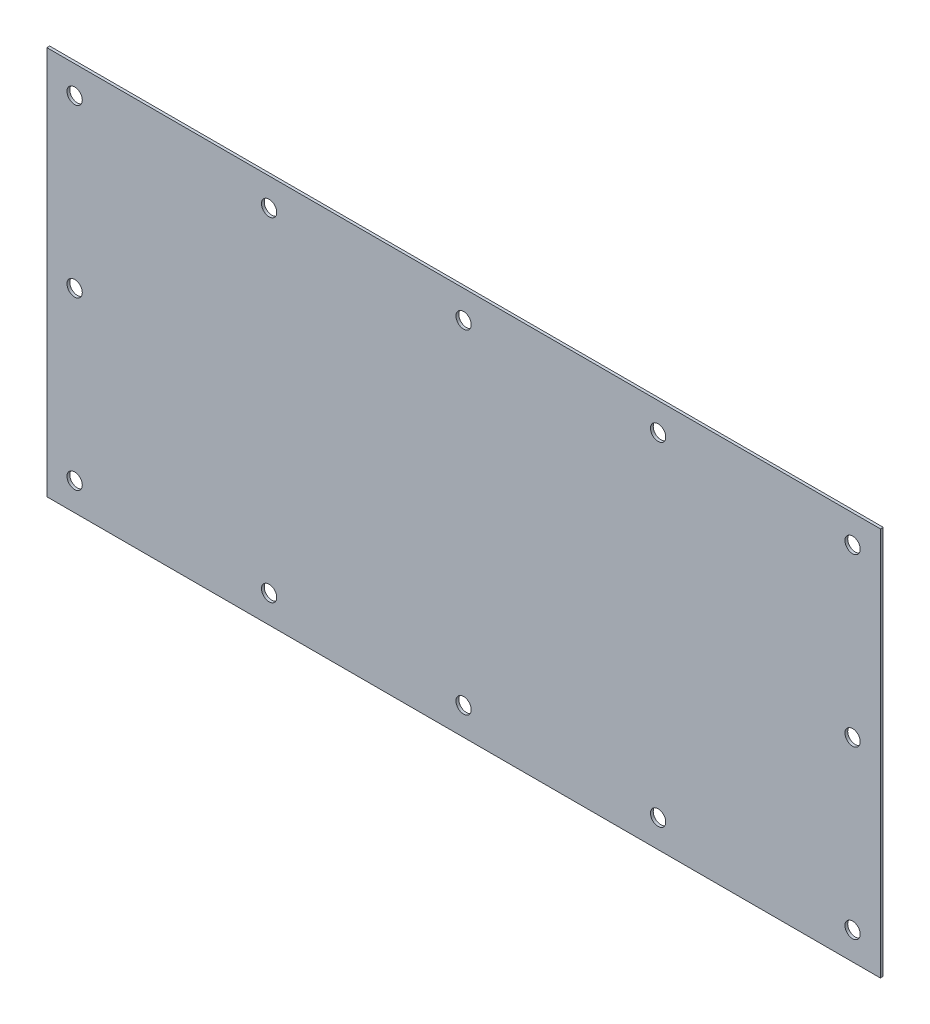
SolidWorks part; units mm, degrees
ref_plane "정면" through (0, 0, 0) normal (0, 0, 1) x (1, 0, 0)
ref_plane "윗면" through (0, 0, 0) normal (0, 1, 0) x (1, 0, 0)
ref_plane "우측면" through (0, 0, 0) normal (1, 0, 0) x (0, 0, -1)
sketch "스케치1" plane through (0, 0, 0) normal (0, 0, 1) x (1, 0, 0)
  line L1 (-150, -70) -> (150, -70)
  line L2 (-150, -70) -> (-150, 70)
  line L3 (-150, 70) -> (150, 70)
  line L4 (150, -70) -> (150, 70)
  line L5 (-150, -70) -> (150, 70) construction
  line L6 (-150, 70) -> (150, -70) construction
  line L7 (-140, -60) -> (140, -60) construction
  line L8 (-140, -60) -> (-140, 60) construction
  line L9 (-140, 60) -> (140, 60) construction
  line L10 (140, -60) -> (140, 60) construction
  line L11 (-140, -60) -> (140, 60) construction
  line L12 (-140, 60) -> (140, -60) construction
  point P0 (0, 0)
  point P6 (0, 0)
  point P12 (-140, 60)
  point P13 (140, 60)
  point P14 (140, -60)
  point P15 (-140, -60)
  point P16 (0, -60)
  point P17 (-70, -60)
  point P19 (70, -60)
  point P22 (0, 60)
  point P23 (-70, 60)
  point P25 (70, 60)
  point P26 (-140, 0)
  point P27 (0, 60)
  point P33 (140, 0)
  dimension "D1" = 300
  dimension "D2" = 140
  dimension "D3" = 10
  dimension "D4" = 10
  dimension "D7" = 70
  dimension "D8" = 70
extrude "보스-돌출1" add sketch "스케치1" along normal blind 1 contours L3 L4 L1 L2
hole_wizard "M5 여유 구멍1" positions "스케치2" profile "스케치3" hole size "M5" standard "KS" end condition through all
sketch "스케치2" plane through (0, 0, 0) normal (0, 0, -1) x (-1, 0, 0)
  point P0 (-140, 60)
  point P3 (-70, 60)
  point P6 (70, 60)
  point P9 (0, 60)
  point P18 (140, 60)
  point P27 (140, 0)
  point P36 (140, -60)
  point P45 (-140, 0)
  point P54 (-140, -60)
  point P57 (-70, -60)
  point P60 (70, -60)
  point P63 (0, -60)
sketch "스케치3" plane through (140, 60, 0) normal (1, 0, 0) x (0, 1, 0)
  line L0 (0, 0) -> (0, 1)
  line L1 (0, 1) -> (2.75, 1)
  line L2 (2.75, 1) -> (2.75, 0)
  line L5 (2.75, 0) -> (0, 0)
  line L11 (0, -6.35) -> (0, 107.95) construction
  dimension "관통 구멍 지름" = 5.5
  dimension "관통 구멍 깊이" = 1
